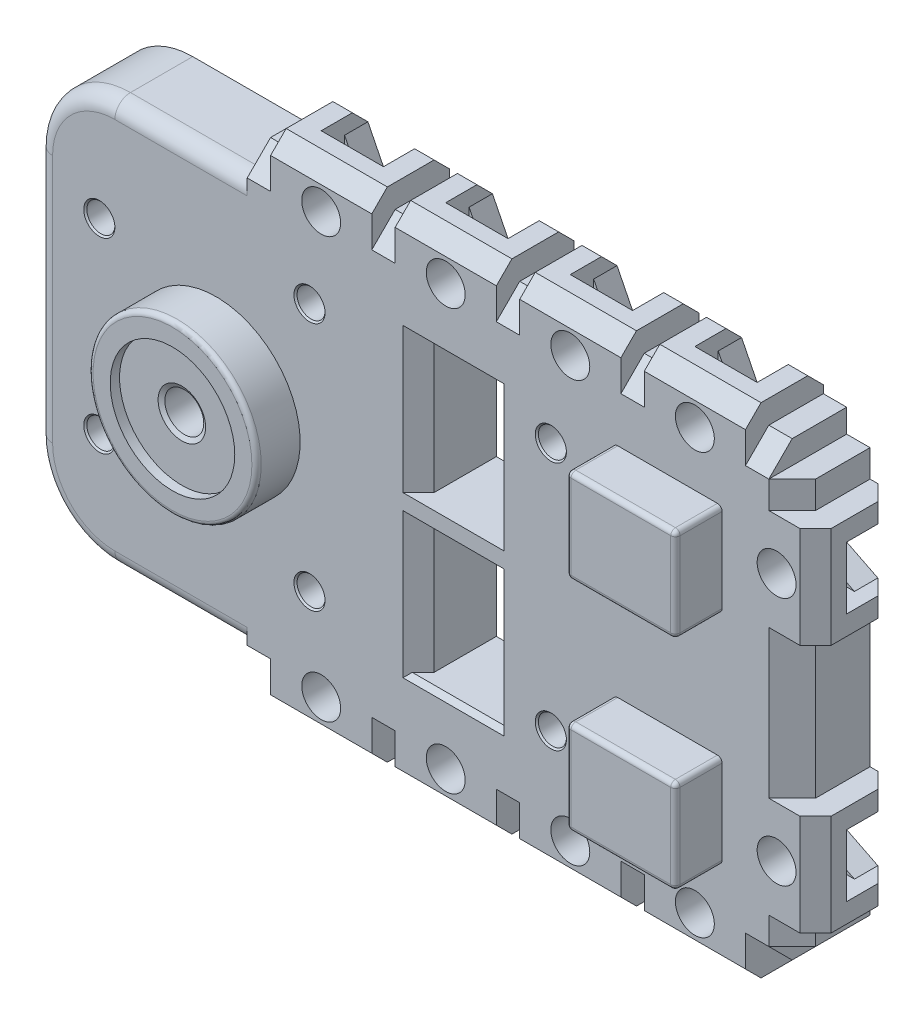
SolidWorks part; units mm, degrees
ref_plane "Front" through (0, 0, 0) normal (0, 0, 1) x (1, 0, 0)
ref_plane "Top" through (0, 0, 0) normal (0, 1, 0) x (1, 0, 0)
ref_plane "Right" through (0, 0, 0) normal (1, 0, 0) x (0, 0, -1)
sketch "Sketch1" plane through (0, 0, 0) normal (0, 0, 1) x (1, 0, 0)
  line L0 (12.75, 0) -> (38.5, 0) construction
  line L1 (37, -13) -> (35.5, -13)
  line L2 (37, -13) -> (37, -11.25)
  line L3 (37, 13) -> (35.5, 13)
  line L4 (-11.5, -13) -> (-11.5, 13)
  line L5 (37, -13) -> (-11.5, 13) construction
  line L6 (37, 13) -> (-11.5, -13) construction
  line L7 (37, -4.75) -> (38.5, -4.75)
  line L8 (38.5, -11.25) -> (38.5, -4.75)
  line L9 (37, -11.25) -> (38.5, -11.25)
  line L10 (37, -4.75) -> (37, 4.75)
  line L11 (2, 13) -> (-11.5, 13)
  line L12 (2, 13) -> (2, 14.5)
  line L13 (35.5, 13) -> (35.5, 14.5)
  line L14 (2, 14.5) -> (3.5, 14.5)
  line L15 (37, 11.25) -> (37, 13)
  line L16 (37, 11.25) -> (38.5, 11.25)
  line L17 (37, 4.75) -> (38.5, 4.75)
  line L18 (38.5, 11.25) -> (38.5, 4.75)
  line L19 (35.5, -13) -> (35.5, -14.5)
  line L20 (34, -14.5) -> (35.5, -14.5)
  line L21 (34, -14.5) -> (34, -16)
  line L22 (34, -16) -> (27.5, -16)
  line L23 (34, 14.5) -> (35.5, 14.5)
  line L24 (34, 14.5) -> (34, 16)
  line L25 (27.5, 14.5) -> (27.5, 16)
  line L26 (34, 16) -> (27.5, 16)
  line L27 (26, 14.5) -> (27.5, 14.5)
  line L28 (26, 14.5) -> (26, 16)
  line L29 (19.5, 14.5) -> (19.5, 16)
  line L30 (26, 16) -> (19.5, 16)
  line L31 (18, 14.5) -> (19.5, 14.5)
  line L32 (18, 14.5) -> (18, 16)
  line L33 (11.5, 14.5) -> (11.5, 16)
  line L34 (18, 16) -> (11.5, 16)
  line L35 (10, 14.5) -> (11.5, 14.5)
  line L36 (10, 14.5) -> (10, 16)
  line L37 (3.5, 14.5) -> (3.5, 16)
  line L38 (10, 16) -> (3.5, 16)
  line L39 (27.5, -14.5) -> (27.5, -16)
  line L40 (26, -14.5) -> (27.5, -14.5)
  line L41 (26, -14.5) -> (26, -16)
  line L42 (26, -16) -> (19.5, -16)
  line L43 (19.5, -14.5) -> (19.5, -16)
  line L44 (18, -14.5) -> (19.5, -14.5)
  line L45 (18, -14.5) -> (18, -16)
  line L46 (18, -16) -> (11.5, -16)
  line L47 (11.5, -14.5) -> (11.5, -16)
  line L48 (10, -14.5) -> (11.5, -14.5)
  line L49 (10, -14.5) -> (10, -16)
  line L50 (10, -16) -> (3.5, -16)
  line L51 (3.5, -14.5) -> (3.5, -16)
  line L52 (2, -14.5) -> (3.5, -14.5)
  line L53 (2, -13) -> (2, -14.5)
  line L54 (2, -13) -> (-11.5, -13)
  point P0 (12.75, 0)
  dimension "D1" = 48.5
  dimension "D2" = 26
  dimension "D3" = 11.5
  dimension "D4" = 1.5
  dimension "D5" = 33.5
  dimension "D6" = 1.5
  dimension "D7" = 1.5
  dimension "D8" = 6.5
  dimension "D9" = 22.5
  dimension "D10" = 1.5
  dimension "D11" = 6.5
  dimension "D12" = 1.5
  dimension "D13" = 1.5
extrude "Boss-Extrude1" add sketch "Sketch1" along normal mid plane 5
sketch "Sketch4" plane through (0, 0, 2.5) normal (0, 0, 1) x (1, 0, 0)
  line L0 (-11.5, 13) -> (-11.5, -13) construction
  line L1 (32.5, -10) -> (-11.5, -10)
  line L2 (32.5, -10) -> (32.5, 10)
  line L3 (32.5, 10) -> (-11.5, 10)
  line L4 (-11.5, -10) -> (-11.5, 10)
  line L5 (32.5, -10) -> (-11.5, 10) construction
  line L6 (32.5, 10) -> (-11.5, -10) construction
  point P0 (10.5, 0)
  dimension "D1" = 20
  dimension "D2" = 44
sketch "Sketch5" plane through (0, 0, 2.5) normal (0, 0, 1) x (1, 0, 0)
  line L1 (32.5, 10) -> (25.5, 10)
  line L2 (32.5, 10) -> (32.5, 4)
  line L3 (25.5, -10) -> (25.5, -4)
  line L4 (25.5, 10) -> (25.5, 4)
  line L5 (32.5, -10) -> (25.5, -10)
  line L6 (37, -4.75) -> (37, 4.75) construction
  line L7 (25.5, 4) -> (32.5, 4)
  line L8 (0, 0) -> (35.7232, 0) construction
  line L9 (32.5, -10) -> (32.5, -4)
  line L10 (25.5, -4) -> (32.5, -4)
  dimension "D2" = 4.5
  dimension "D1" = 7
  dimension "D3" = 20
  dimension "D4" = 8
extrude "Boss-Extrude3" add sketch "Sketch5" along normal blind 3
sketch "Sketch6" plane through (38.5, 0, 0) normal (1, 0, 0) x (0, 0, -1)
  line L0 (2.5, 4.75) -> (2.5, 11.25) construction
  line L1 (-0.5, 10) -> (2.5, 10)
  line L2 (-0.5, 10) -> (-0.5, 6)
  line L3 (-0.5, 6) -> (2.5, 6)
  line L4 (2.5, 10) -> (2.5, 6)
  line L5 (-0.5, 10) -> (2.5, 6) construction
  line L6 (-0.5, 6) -> (2.5, 10) construction
  line L7 (-2.5, 8) -> (1, 8) construction
  line L8 (-2.5, 4.75) -> (-2.5, 11.25) construction
  point P0 (1, 8)
  dimension "D1" = 4
  dimension "D2" = 2
extrude "Cut-Extrude3" cut sketch "Sketch6" against normal blind 1
sketch "Sketch7" plane through (0, 0, 0.5) normal (0, 0, -1) x (-1, 0, 0)
  line L0 (-37.5, 10) -> (-38.5, 10) construction
  line L1 (-37.1547, 10) -> (-38.3094, 8) construction
  line L2 (-38.3094, 8) -> (-37.1547, 6) construction
  line L3 (-37.1547, 6) -> (-34.8453, 6)
  line L6 (-34.8453, 6) -> (-33.6906, 8)
  line L7 (-33.6906, 8) -> (-34.8453, 10)
  line L8 (-34.8453, 10) -> (-37.1547, 10)
  line L9 (-37.5, 8) -> (-36, 8) construction
  line L10 (-37.5, 6) -> (-37.5, 10) construction
  line L11 (-38.5, 10) -> (-38.5, 6) construction
  line L12 (-37.1547, 10) -> (-38.5, 10)
  line L13 (-38.5, 10) -> (-38.5, 6)
  line L14 (-38.5, 6) -> (-37.1547, 6)
  circle A0 centre (-36, 8) radius 2 construction
  dimension "D1" = 2.5
extrude "Cut-Extrude4" cut sketch "Sketch7" along normal blind 1.5
sketch "Sketch8" plane through (0, 0, -2.5) normal (0, 0, -1) x (-1, 0, 0)
  line L0 (-37.5, 10) -> (-35.5, 9)
  line L1 (-35.5, 9) -> (-35.5, 7)
  line L2 (-35.5, 7) -> (-37.5, 6)
  line L3 (-34.8453, 6) -> (-38.5, 6) construction
  line L4 (-37.5, 6) -> (-38.5, 6) construction
  line L5 (-37.5, 8) -> (-35.5, 8) construction
  line L6 (-37.5, 6) -> (-37.5, 10) construction
  line L7 (-37, -4.75) -> (-37, 4.75) construction
  line L8 (-37.5, 10) -> (-37.5, 6)
  dimension "D1" = 2
  dimension "D2" = 1.5
extrude "Cut-Extrude5" cut sketch "Sketch8" against normal up to next (1.5 mm away)
sketch "Sketch10" plane through (0, 16, 0) normal (0, 1, 0) x (1, 0, 0)
  line L0 (28.75, -0.5) -> (28.75, 2.5)
  line L1 (28.75, -0.5) -> (32.75, -0.5)
  line L2 (32.75, -0.5) -> (32.75, 2.5)
  line L3 (28.75, 2.5) -> (32.75, 2.5)
  line L4 (28.75, -0.5) -> (32.75, 2.5) construction
  line L5 (32.75, -0.5) -> (28.75, 2.5) construction
  line L6 (30.75, -2.5) -> (30.75, 1) construction
  line L7 (34, -2.5) -> (27.5, -2.5) construction
  line L8 (34, 2.5) -> (27.5, 2.5) construction
  point P0 (30.75, 1)
  dimension "D1" = 4
  dimension "D2" = 3
extrude "Cut-Extrude6" cut sketch "Sketch10" against normal blind 1
sketch "Sketch11" plane through (0, 0, 0.5) normal (0, 0, -1) x (-1, 0, 0)
  line L0 (-30.75, 16) -> (-30.75, 13.5) construction
  line L1 (-30.75, 15.8094) -> (-32.75, 14.6547) construction
  line L2 (-32.75, 14.6547) -> (-32.75, 12.3453)
  line L3 (-32.75, 12.3453) -> (-30.75, 11.1906)
  line L4 (-30.75, 11.1906) -> (-28.75, 12.3453)
  line L5 (-28.75, 12.3453) -> (-28.75, 14.6547)
  line L6 (-28.75, 14.6547) -> (-30.75, 15.8094) construction
  line L7 (-28.75, 16) -> (-32.75, 16) construction
  line L8 (-34, 16) -> (-32.75, 16) construction
  line L9 (-28.75, 14.6547) -> (-28.75, 16)
  line L10 (-28.75, 16) -> (-32.75, 16)
  line L11 (-32.75, 16) -> (-32.75, 14.6547)
  circle A0 centre (-30.75, 13.5) radius 2 construction
  dimension "D1" = 4
  dimension "D2" = 2.5
extrude "Cut-Extrude7" cut sketch "Sketch11" along normal blind 1.5
sketch "Sketch12" plane through (0, 0, -2.5) normal (0, 0, -1) x (-1, 0, 0)
  line L0 (-28.75, 15) -> (-29.75, 13)
  line L1 (-29.75, 13) -> (-31.75, 13)
  line L2 (-31.75, 13) -> (-32.75, 15)
  line L3 (-30.75, 15) -> (-30.75, 13) construction
  line L4 (-32.75, 15) -> (-28.75, 15) construction
  line L5 (-35.5, 14.5) -> (-34, 14.5) construction
  line L6 (-32.75, 15) -> (-28.75, 15)
  dimension "D1" = 1.5
  dimension "D2" = 2
extrude "Cut-Extrude8" cut sketch "Sketch12" against normal up to next (1.5 mm away)
sketch "Sketch13" plane through (0, 0, 2.5) normal (0, 0, 1) x (1, 0, 0)
  circle A0 centre (36, 8) radius 1.25
  dimension "D1" = 2.5
extrude "Cut-Extrude9" cut sketch "Sketch13" against normal up to next (2 mm away)
sketch "Sketch14" plane through (0, 0, 2.5) normal (0, 0, 1) x (1, 0, 0)
  circle A0 centre (30.75, 13.5) radius 1.25
  dimension "D1" = 2.5
extrude "Cut-Extrude10" cut sketch "Sketch14" against normal up to next (2 mm away)
pattern_linear "LPattern1" count 4 spacing 8 along (-1, 0, 0) of "Cut-Extrude6", "Cut-Extrude7", "Cut-Extrude8", "Cut-Extrude10"
mirror "Mirror1" about plane through (0, 0, 0) normal (0, 1, 0) of "LPattern1", "Cut-Extrude10", "Cut-Extrude9", "Cut-Extrude8", "Cut-Extrude7", "Cut-Extrude6", "Cut-Extrude5", "Cut-Extrude4", "Cut-Extrude3"
fillet "Fillet1" radius 5 2 edges at (-11.5, -13, 0) (-11.5, 13, 0)
sketch "Sketch15" plane through (0, 0, 2.5) normal (0, 0, 1) x (1, 0, 0)
  line L0 (0, 0) -> (38.4863, 0) construction
  line L1 (38.5, 4.75) -> (38.5, 11.25) construction
  line L3 (-7.25, 9.25) -> (-7.25, 14.1999)
  line L4 (-7.25, 14.1999) -> (-13.5472, 14.1999)
  line L5 (-13.5472, 14.1999) -> (-13.5472, 7.5)
  line L6 (-13.5472, 7.5) -> (-9, 7.5)
  line L7 (-13.5472, -14.1999) -> (-13.5472, -7.5)
  line L8 (-7.25, -14.1999) -> (-13.5472, -14.1999)
  line L9 (-7.25, -9.25) -> (-7.25, -14.1999)
  line L10 (-13.5472, -7.5) -> (-9, -7.5)
  line L11 (-11.5, -10) -> (-11.5, 10) construction
  circle A0 centre (33, 10.4) radius 1.75
  circle A1 centre (33, -10.4) radius 1.75
  arc A2 (-9, 7.5) -> (-7.25, 9.25) centre (-9, 9.25) ccw
  circle A3 centre (33, -10.4) radius 1.75
  arc A4 (-9, -7.5) -> (-7.25, -9.25) centre (-9, -9.25) cw
  dimension "D1" = 20.8
  dimension "D2" = 5.5
  dimension "D3" = 3.5
  dimension "D4" = 18.5
  dimension "D5" = 2.5
sketch "Sketch2" plane through (0, 0, 2.5) normal (0, 0, 1) x (1, 0, 0)
  line L0 (0, 0) -> (23.4398, 0) construction
  line L1 (13, 9.5) -> (17.5, 9.5)
  line L2 (13, 9.5) -> (13, 0.5)
  line L3 (13, 0.5) -> (17.5, 0.5)
  line L4 (17.5, 9.5) -> (17.5, 0.5)
  line L5 (13, 9.5) -> (17.5, 0.5) construction
  line L6 (13, 0.5) -> (17.5, 9.5) construction
  line L7 (13, -9.5) -> (13, -0.5)
  line L8 (13, -9.5) -> (17.5, -9.5)
  line L9 (17.5, -9.5) -> (17.5, -0.5)
  line L10 (13, -0.5) -> (17.5, -0.5)
  point P0 (15.25, 5)
  dimension "D1" = 4.5
  dimension "D2" = 9
  dimension "D3" = 13
  dimension "D4" = 19
extrude "Cut-Extrude1" cut sketch "Sketch2" against normal through all
sketch "Sketch3" plane through (0, 0, 2.5) normal (0, 0, 1) x (1, 0, 0)
  circle A0 centre (0, 0) radius 5.4
  dimension "D1" = 10.8
extrude "Boss-Extrude4" add sketch "Sketch3" along normal blind 2.8
sketch "Sketch17" plane through (0, 0, 5.3) normal (0, 0, 1) x (1, 0, 0)
  circle A0 centre (0, 0) radius 4
  dimension "D1" = 8
extrude "Cut-Extrude13" cut sketch "Sketch17" against normal blind 0.6
hole_wizard "Ø1.6 (1.6) Diameter Hole1" positions "Sketch19" profile "Sketch18" hole size "Ø1.6" standard "ISO"
sketch "Sketch19" plane through (0, 0, -2.5) normal (0, 0, -1) x (-1, 0, 0)
  point P0 (-33, 10.4)
  point P3 (-33, -10.4)
  point P6 (9, 9.25)
  point P9 (9, -9.25)
sketch "Sketch18" plane through (33, 10.4, -2.5) normal (1, 0, 0) x (0, 1, 0)
  line L0 (0, 0) -> (0, 4.9807)
  line L1 (0, 4.9807) -> (0.8, 4.5)
  line L2 (0.8, 4.5) -> (0.8, 0.0577)
  line L3 (0.8, 0.0577) -> (0.9, 0)
  line L5 (0.9, 0) -> (0, 0)
  line L6 (-0.8, 0.0577) -> (-0.9, 0) construction
  line L10 (0, 4.9807) -> (-0.8, 4.5) construction
  line L11 (0, -6.35) -> (0, 107.95) construction
  dimension "Hole Dia." = 1.6
  dimension "Hole Depth" = 4.5
  dimension "Near C'Sink Dia." = 1.8
  dimension "Near C'Sink Angle" = 120
  dimension "Drill Angle" = 118
hole_wizard "M3 Tapped Hole1" positions "Sketch21" profile "Sketch22" tap size "M3" standard "ISO" end condition through all
sketch "Sketch21" plane through (0, 0, 4.7) normal (0, 0, 1) x (1, 0, 0)
  point P0 (0, 0)
sketch "Sketch22" plane through (0, 0, 4.7) normal (1, 0, 0) x (0, -1, 0)
  line L0 (0, 0) -> (0, 7.2)
  line L1 (0, 7.2) -> (1.25, 7.2)
  line L2 (1.25, 7.2) -> (1.25, 0.1588)
  line L3 (1.25, 0.1588) -> (1.525, 0)
  line L5 (1.525, 0) -> (0, 0)
  line L6 (-1.25, 0.1588) -> (-1.525, 0) construction
  line L11 (0, -6.35) -> (0, 107.95) construction
  dimension "Thru Tap Drill Dia." = 2.5
  dimension "Thru Tap Drill Depth" = 7.2
  dimension "Near C'Sink Dia." = 3.05
  dimension "Near C'Sink Angle" = 120
cosmetic thread "Hole Thread1" parameters "D2"=3
hole_wizard "Ø1.8 (1.8) Diameter Hole1" positions "Sketch24" profile "Sketch25" hole size "Ø1.8" standard "ISO" end condition through all
sketch "Sketch24" plane through (0, 0, 2.5) normal (0, 0, 1) x (1, 0, 0)
  line L0 (0, 0) -> (35.0384, 0) construction
  point P0 (6, 8)
  point P7 (21.5, 8)
  point P9 (-7.5, 6)
  point P14 (21.5, -8)
  point P15 (6, -8)
  point P16 (-7.5, -6)
  dimension "D1" = 16
  dimension "D2" = 6
  dimension "D3" = 15.5
  dimension "D4" = 12
  dimension "D5" = 7.5
sketch "Sketch25" plane through (6, 8, 2.5) normal (1, 0, 0) x (0, -1, 0)
  line L0 (0, 0) -> (0, 5)
  line L1 (0, 5) -> (0.9, 5)
  line L2 (0.9, 5) -> (0.9, 0.1)
  line L3 (0.9, 0.1) -> (1, 0)
  line L5 (1, 0) -> (0, 0)
  line L6 (-0.9, 0.1) -> (-1, 0) construction
  line L11 (0, -6.35) -> (0, 107.95) construction
  dimension "Thru Hole Dia." = 1.8
  dimension "Thru Hole Depth" = 5
  dimension "Near C'Sink Dia." = 2
  dimension "Near C'Sink Angle" = 90
fillet "Fillet2" radius 1 5 edges at (-2.25, 13, 2.5) (-10.0355, 11.5355, 2.5) (-11.5, 0, 2.5) (-10.0355, -11.5355, 2.5) (-2.25, -13, 2.5)
chamfer "Chamfer1" distance 1 angle 45 30 edges at (4.125, -16, -2.5) (9.375, -16, -2.5) (12.125, -16, -2.5) (17.375, -16, -2.5) (20.125, -16, -2.5) (25.375, -16, -2.5) (28.125, -16, -2.5) (33.375, -16, -2.5) (4.125, 16, -2.5) (9.375, 16, -2.5) (12.125, 16, -2.5) (17.375, 16, -2.5) (20.125, 16, -2.5) (25.375, 16, -2.5) (28.125, 16, -2.5) (33.375, 16, -2.5) (38.5, -10.625, -2.5) (38.5, -5.375, -2.5) (38.5, 5.375, -2.5) (38.5, 10.625, -2.5) (6.75, 16, 2.5) (14.75, 16, 2.5) (22.75, 16, 2.5) (30.75, 16, 2.5) (38.5, 8, 2.5) (38.5, -8, 2.5) (30.75, -16, 2.5) (22.75, -16, 2.5) (14.75, -16, 2.5) (6.75, -16, 2.5)
chamfer "Chamfer2" distance 1.5 angle 45 13 edges at (2.75, 14.5, 2.5) (10.75, 14.5, 2.5) (18.75, 14.5, 2.5) (26.75, 14.5, 2.5) (34.75, 14.5, 2.5) (37, 12.125, 2.5) (2.75, -14.5, 2.5) (10.75, -14.5, 2.5) (18.75, -14.5, 2.5) (26.75, -14.5, 2.5) (37, -12.125, 2.5) (34.75, -14.5, 2.5) (37, 0, 2.5)
chamfer "Chamfer3" distance 1 angle 45 4 edges at (13, 5, 2.5) (17.5, 5, 2.5) (17.5, -5, 2.5) (13, -5, 2.5)
chamfer "Chamfer4" distance 0.3 angle 45 2 edges at (15.25, 9.5, 2.5) (15.25, -9.5, 2.5)
fillet "Fillet3" radius 0.3 17 edges at (29, 4, 5.5) (25.5, 7, 5.5) (29, 10, 5.5) (32.5, 7, 5.5) (25.5, -7, 5.5) (29, -4, 5.5) (32.5, -7, 5.5) (29, -10, 5.5) (5.4, 0, 5.3) (25.5, 10, 4) (32.5, 10, 4) (32.5, 4, 4) (25.5, 4, 4) (25.5, -4, 4) (32.5, -4, 4) (32.5, -10, 4) (25.5, -10, 4)
